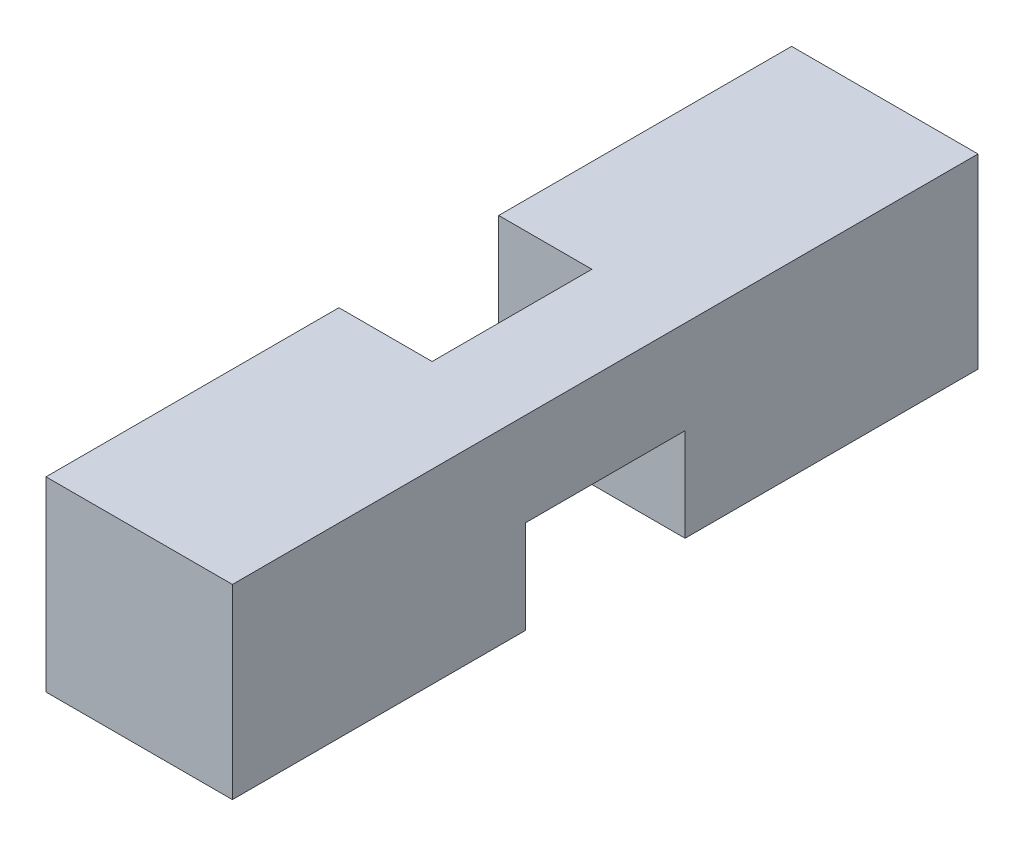
SolidWorks part; units mm, degrees
ref_plane "Front Plane" through (0, 0, 0) normal (0, 0, 1) x (1, 0, 0)
ref_plane "Top Plane" through (0, 0, 0) normal (0, 1, 0) x (1, 0, 0)
ref_plane "Right Plane" through (0, 0, 0) normal (1, 0, 0) x (0, 0, -1)
sketch "Sketch1" plane through (0, 0, 0) normal (0, 0, 1) x (1, 0, 0)
  line L1 (-1.75, 1.75) -> (1.75, 1.75)
  line L2 (-1.75, 1.75) -> (-1.75, -1.75)
  line L3 (-1.75, -1.75) -> (1.75, -1.75)
  line L4 (1.75, 1.75) -> (1.75, -1.75)
  line L5 (-1.75, 1.75) -> (1.75, -1.75) construction
  line L6 (-1.75, -1.75) -> (1.75, 1.75) construction
  point P0 (0, 0)
  dimension "D1" = 3.5
  dimension "D2" = 3.5
extrude "Boss-Extrude1" add sketch "Sketch1" along normal blind 14
ref_plane "Plane1" through (0, 0, 7) normal (0, 0, 1) x (1, 0, 0)
sketch "Sketch2" plane through (0, 0, 7) normal (0, 0, 1) x (1, 0, 0)
  line L0 (0, 0) -> (1.75, 0) construction
  line L1 (1.75, -1.75) -> (1.75, 1.75) construction
  line L6 (1.75, -1.75) -> (1.75, 1.75)
  line L7 (-1.75, -1.75) -> (1.75, -1.75)
  line L8 (-1.75, 1.75) -> (-1.75, -1.75)
  line L9 (1.75, 1.75) -> (-1.75, 1.75)
  line L10 (1.75, -1.75) -> (1.75, 0)
  line L11 (-1.75, -1.75) -> (1.75, -1.75)
  line L12 (-1.75, 1.75) -> (-1.75, -1.75)
  line L13 (0, 1.75) -> (-1.75, 1.75)
  arc A0 (0, 1.75) -> (1.75, 0) centre (1.75, 1.75) ccw
  dimension "D1" = 0
extrude "Cut-Extrude1" cut sketch "Sketch2" against normal blind 1.5 and the other way blind 1.5
